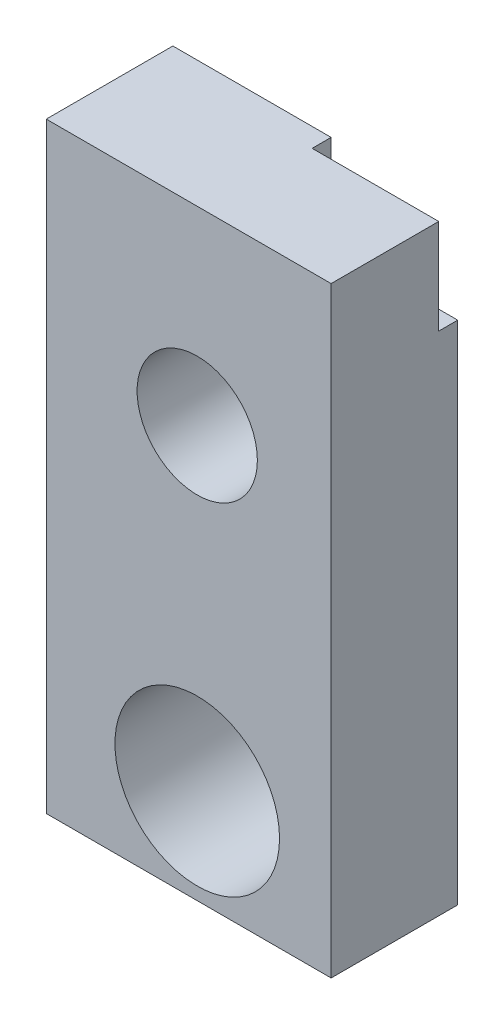
SolidWorks part; units mm, degrees
ref_plane "Ebene vorne" through (0, 0, 0) normal (0, 0, 1) x (1, 0, 0)
ref_plane "Ebene oben" through (0, 0, 0) normal (0, 1, 0) x (1, 0, 0)
ref_plane "Ebene rechts" through (0, 0, 0) normal (1, 0, 0) x (0, 0, -1)
sketch "Skizze1" plane through (0, 0, 0) normal (0, 0, 1) x (1, 0, 0)
  line L1 (0, 0) -> (43, 0)
  line L2 (0, 0) -> (0, 95)
  line L3 (0, 95) -> (43, 95)
  line L4 (43, 0) -> (43, 95)
  dimension "D1" = 43
  dimension "D2" = 95
extrude "Aufsatz-Linear austragen1" add sketch "Skizze1" along normal blind 20
sketch "Skizze2" plane through (0, 0, 20) normal (0, 0, 1) x (1, 0, 0)
  line L0 (43, 0) -> (43, 95) construction
  line L1 (43, 95) -> (0, 95) construction
  circle A0 centre (21.85, 15) radius 13
  dimension "D1" = 26
  dimension "D2" = 21.15
  dimension "D3" = 80
extrude "Schnitt-Linear austragen1" cut sketch "Skizze2" against normal blind 34
sketch "Skizze3" plane through (0, 0, 20) normal (0, 0, 1) x (1, 0, 0)
  line L0 (43, 0) -> (43, 95) construction
  line L1 (43, 95) -> (0, 95) construction
  circle A0 centre (21.85, 65) radius 9.5
  dimension "D1" = 19
  dimension "D2" = 21.15
  dimension "D3" = 30
extrude "Schnitt-Linear austragen2" cut sketch "Skizze3" against normal blind 34
sketch "Skizze4" plane through (0, 95, 0) normal (0, 1, 0) x (1, 0, 0)
  line L1 (43, 0) -> (23, 0)
  line L2 (43, 0) -> (43, -3)
  line L3 (43, -3) -> (23, -3)
  line L4 (23, 0) -> (23, -3)
  dimension "D1" = 20
  dimension "D2" = 3
extrude "Schnitt-Linear austragen3" cut sketch "Skizze4" against normal blind 15
sketch "Skizze8" plane through (0, 0, 3) normal (0, 0, -1) x (-1, 0, 0)
  line L0 (-43, 80) -> (-23, 80) construction
  line L1 (-43, 80) -> (-43, 95) construction
  circle A0 centre (-38, 86) radius 1.62
  dimension "D1" = 3.24
  dimension "D2" = 6
  dimension "D3" = 5
extrude "Schnitt-Linear austragen6" cut sketch "Skizze8" against normal blind 5
cosmetic thread "Gewindedarstellung3" parameters "D1"=5, "D2"=4
sketch "Skizze9" plane through (0, 0, 3) normal (0, 0, -1) x (-1, 0, 0)
  line L0 (-23, 80) -> (-23, 95) construction
  line L1 (-43, 80) -> (-23, 80) construction
  circle A0 centre (-28, 86) radius 1.62
  dimension "D1" = 3.24
  dimension "D2" = 5
  dimension "D3" = 6
extrude "Schnitt-Linear austragen7" cut sketch "Skizze9" against normal blind 5
cosmetic thread "Gewindedarstellung4" parameters "D1"=5, "D2"=4
sketch "Skizze10" plane through (0, 0, 0) normal (0, 0, -1) x (-1, 0, 0)
  line L0 (0, 0) -> (-43, 0) construction
  line L1 (0, 95) -> (0, 0) construction
  circle A0 centre (-4.35, 15) radius 1.5
  circle A1 centre (-39.35, 15) radius 1.5
  dimension "D5" = 3
  dimension "D6" = 3
  dimension "D1" = 15
  dimension "D2" = 15
  dimension "D3" = 4.35
  dimension "D4" = 35
extrude "Schnitt-Linear austragen8" cut sketch "Skizze10" against normal blind 12
cosmetic thread "Gewindedarstellung5" parameters "D1"=12, "D2"=4
cosmetic thread "Gewindedarstellung6" parameters "D1"=12, "D2"=4
sketch "Skizze11" plane through (0, 0, 0) normal (-1, 0, 0) x (0, 0, 1)
  line L1 (0, 0) -> (20, 0)
  line L2 (0, 0) -> (0, 95)
  line L3 (0, 95) -> (20, 95)
  line L4 (20, 0) -> (20, 95)
extrude "Aufsatz-Linear austragen2" add sketch "Skizze11" along normal blind 2
